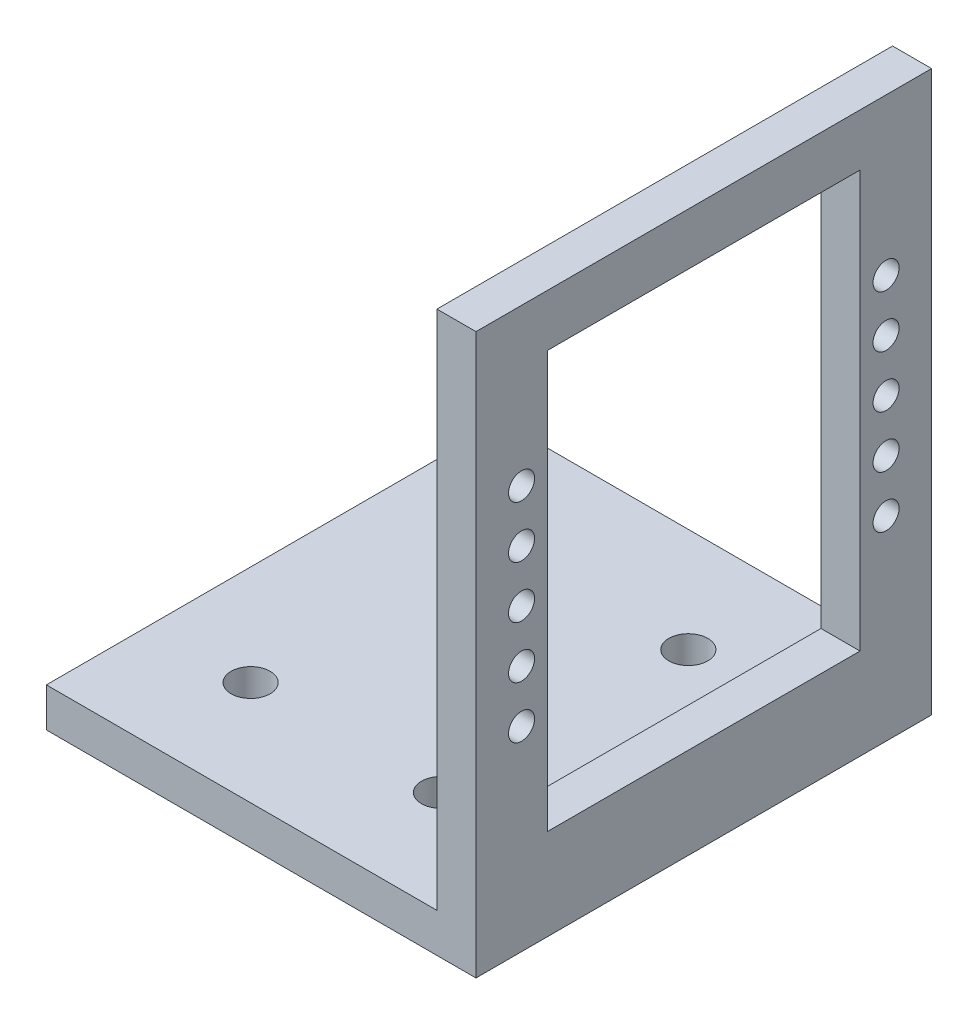
SolidWorks part; units mm, degrees
ref_plane "前视基准面" through (0, 0, 0) normal (0, 0, 1) x (1, 0, 0)
ref_plane "上视基准面" through (0, 0, 0) normal (0, 1, 0) x (1, 0, 0)
ref_plane "右视基准面" through (0, 0, 0) normal (1, 0, 0) x (0, 0, -1)
sketch "草图1" plane through (0, 0, 0) normal (0, 0, 1) x (1, 0, 0)
  line L0 (-33, 0) -> (0, 0)
  line L1 (0, 0) -> (0, 43)
  line L2 (0, 43) -> (-3, 43)
  line L3 (-3, 43) -> (-3, 3)
  line L4 (-3, 3) -> (-33, 3)
  line L5 (-33, 3) -> (-33, 0)
  dimension "D1" = 3
  dimension "D2" = 3
  dimension "D3" = 40
  dimension "D4" = 30
extrude "凸台-拉伸1" add sketch "草图1" along normal blind 35
sketch "草图2" plane through (-3, 0, 0) normal (-1, 0, 0) x (0, 0, 1)
  line L0 (0, 23) -> (35, 23) construction
  line L1 (0, 43) -> (0, 3) construction
  line L2 (35, 43) -> (35, 3) construction
  line L3 (17.5, 43) -> (17.5, 3) construction
  line L4 (35, 43) -> (0, 43) construction
  line L5 (35, 3) -> (0, 3) construction
  line L6 (0, 23) -> (35, 23) construction
  line L7 (35, 0) -> (0, 0) construction
  line L8 (3.5, 43) -> (3.5, 3) construction
  line L9 (31.5, 43) -> (31.5, 3) construction
  line L11 (5.5, 39) -> (29.5, 39)
  line L12 (5.5, 39) -> (5.5, 7)
  line L13 (5.5, 7) -> (29.5, 7)
  line L14 (29.5, 39) -> (29.5, 7)
  circle A0 centre (3.5, 23) radius 1
  circle A1 centre (31.5, 23) radius 1
  circle A2 centre (3.5, 19) radius 1
  circle A3 centre (3.5, 15) radius 1
  circle A4 centre (3.5, 27) radius 1
  circle A5 centre (31.5, 15) radius 1
  circle A6 centre (31.5, 19) radius 1
  circle A7 centre (31.5, 27) radius 1
  circle A8 centre (3.5, 31) radius 1
  circle A9 centre (31.5, 31) radius 1
  circle A10 centre (31.5, 27) radius 1
  point P25 (17.5, 23)
  dimension "D3" = 2
  dimension "D1" = 23
  dimension "D2" = 28
  dimension "D4" = 24
  dimension "D8" = 8
  dimension "D9" = 8
  dimension "D6" = 3
  dimension "D5" = 2
  dimension "D7" = 2
extrude "切除-拉伸1" cut sketch "草图2" against normal through all contours L14 L11 L12 L13 | A8 | A4 | A0 | A2 | A3 | A5 | A6 | A1 | A7 | A9
sketch "草图3" plane through (0, 3, 0) normal (0, 1, 0) x (1, 0, 0)
  line L0 (-33, -17.5) -> (-3, -17.5) construction
  line L1 (-33, -35) -> (-33, 0) construction
  line L2 (-3, -35) -> (-3, 0) construction
  line L3 (-18, 0) -> (-18, -35) construction
  line L4 (-3, 0) -> (-33, 0) construction
  line L5 (-3, -35) -> (-33, -35) construction
  circle A0 centre (-25.311, -8) radius 1.5
  circle A1 centre (-10.689, -8) radius 1.5
  circle A2 centre (-10.689, -27) radius 1.5
  circle A3 centre (-25.311, -27) radius 1.5
  dimension "D1" = 3
  dimension "D2" = 8
extrude "切除-拉伸2" cut sketch "草图3" against normal through all
